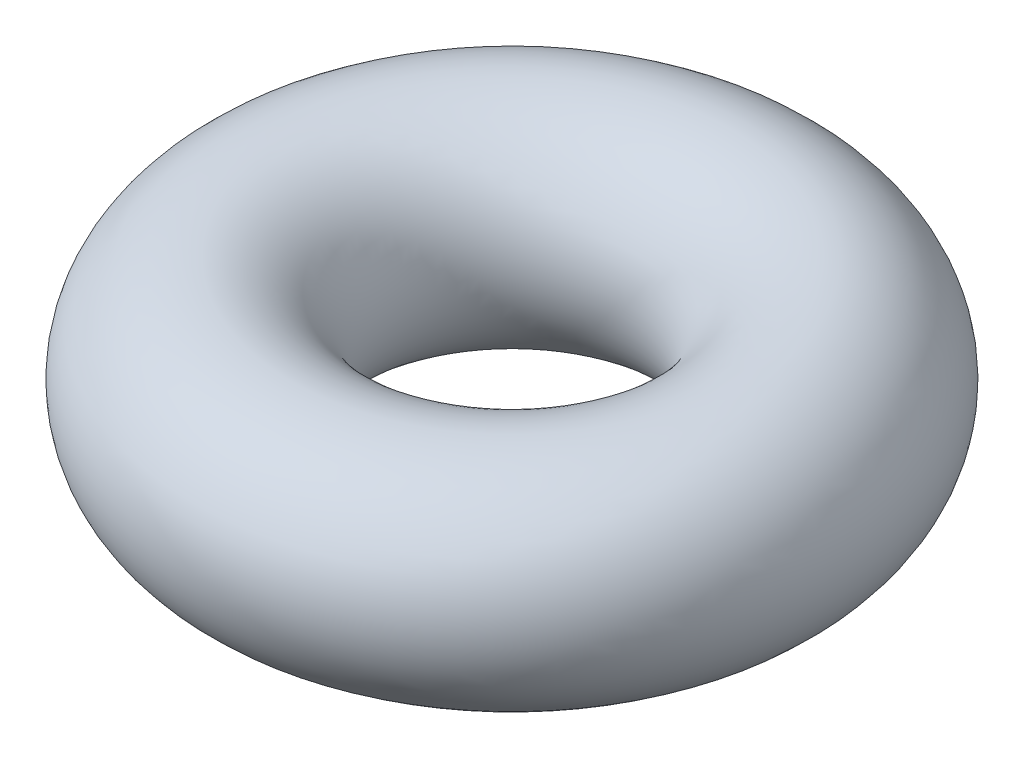
SolidWorks part; units mm, degrees
ref_plane "Front Plane" through (0, 0, 0) normal (0, 0, 1) x (1, 0, 0)
ref_plane "Top Plane" through (0, 0, 0) normal (0, 1, 0) x (1, 0, 0)
ref_plane "Right Plane" through (0, 0, 0) normal (1, 0, 0) x (0, 0, -1)
sketch "Sketch1" plane through (0, 0, 0) normal (0, 0, 1) x (1, 0, 0)
  line L0 (0, 0) -> (1.975, 0) construction
  line L1 (0, 0) -> (0, 3.98) construction
  circle A0 centre (1.975, 0) radius 0.95
  point P5 (1.025, 0)
  point P6 (2.925, 0)
  dimension "D1" = 1.9
  dimension "D2" = 1.025
revolve "Revolve1" add sketch "Sketch1" angle 360 about L1
sketch "Sketch2" plane through (0, 0, 0) normal (0, 1, 0) x (1, 0, 0)
  circle A0 centre (0, 0) radius 0.9949
ref_plane "Plane1" through (0, -0.95, 0) normal (0, 1, 0) x (1, 0, 0)
